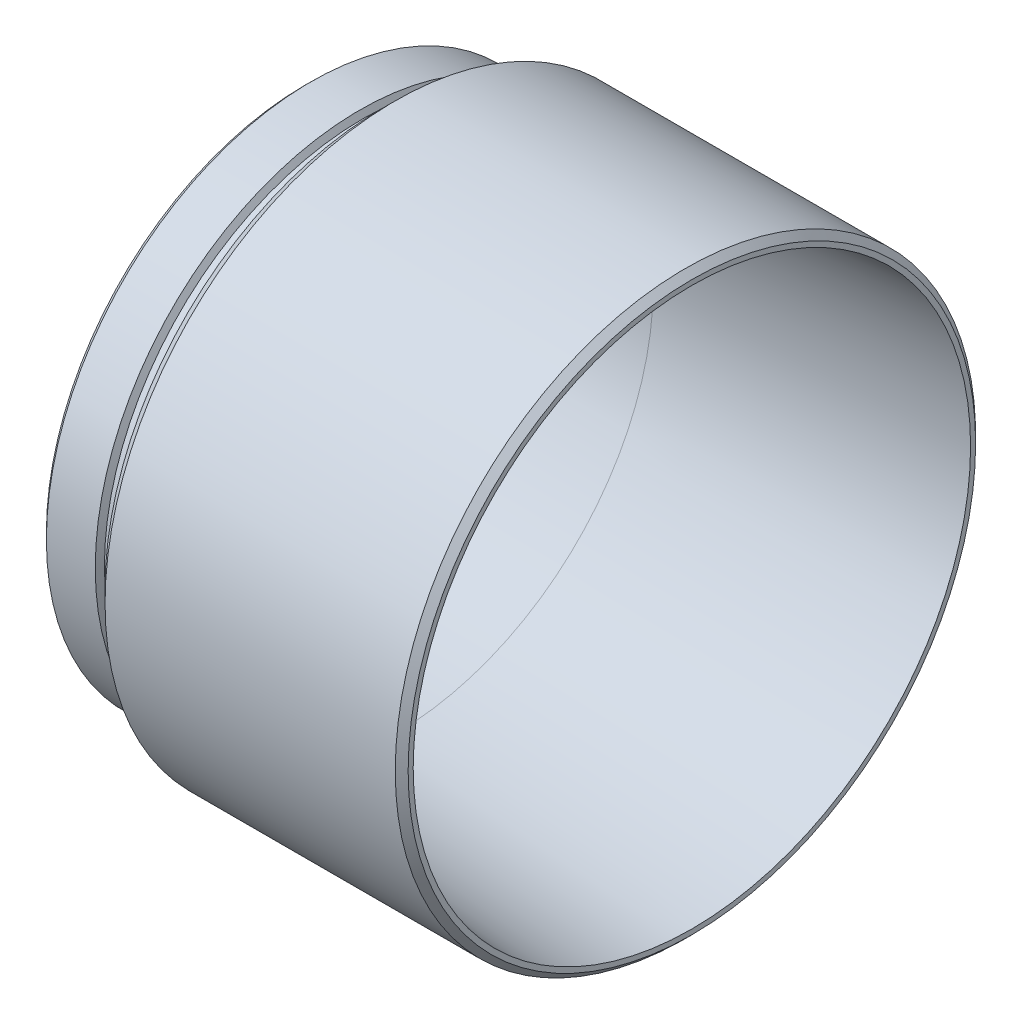
SolidWorks part; units mm, degrees
ref_plane "Plan de face" through (0, 0, 0) normal (0, 0, 1) x (1, 0, 0)
ref_plane "Plan de dessus" through (0, 0, 0) normal (0, 1, 0) x (1, 0, 0)
ref_plane "Plan de droite" through (0, 0, 0) normal (1, 0, 0) x (0, 0, -1)
sketch "Esquisse1" plane through (0, 0, 0) normal (0, 1, 0) x (1, 0, 0)
  line L0 (-32.0943, 0) -> (32.0943, 0) construction
  line L1 (2, 40) -> (-12, 40)
  line L2 (-12, 40) -> (-12, 40.1)
  line L3 (-11.1, 41) -> (-3.5196, 41)
  line L4 (0, 40.6) -> (0, 43)
  line L5 (2, 45) -> (47, 45)
  line L6 (48, 44) -> (48, 43.2166)
  line L7 (48, 43.2166) -> (2, 40)
  line L8 (2, 40) -> (54.1296, 40) construction
  line L13 (-3.5196, 41) -> (-3, 40.1)
  line L14 (-3, 40.1) -> (-0.5, 40.1)
  line L15 (-12, 40.1) -> (-11.1, 41)
  line L16 (0, 43) -> (2, 45)
  line L17 (47, 45) -> (48, 44)
  arc A0 (-0.5, 40.1) -> (0, 40.6) centre (-0.5, 40.6) ccw
  point P4 (0, 0)
  point P17 (0, 45)
  point P20 (48, 45)
  point P30 (-12, 41)
  point P37 (0, 40.1)
  dimension "D17" = 0.5
  dimension "D2" = 4
  dimension "D3" = 2
  dimension "D4" = 48
  dimension "D5" = 12
  dimension "D6" = 45
  dimension "D7" = 41
  dimension "D8" = 1
  dimension "D12" = 0.9
  dimension "D11" = 40.1
  dimension "D9" = 2
  dimension "D10" = 45
  dimension "D14" = 45
  dimension "D13" = 45
  dimension "D15" = 60
  dimension "D16" = 3
  dimension "D18" = 40
revolve "Révolution1" add sketch "Esquisse1" angle 360 about L0
